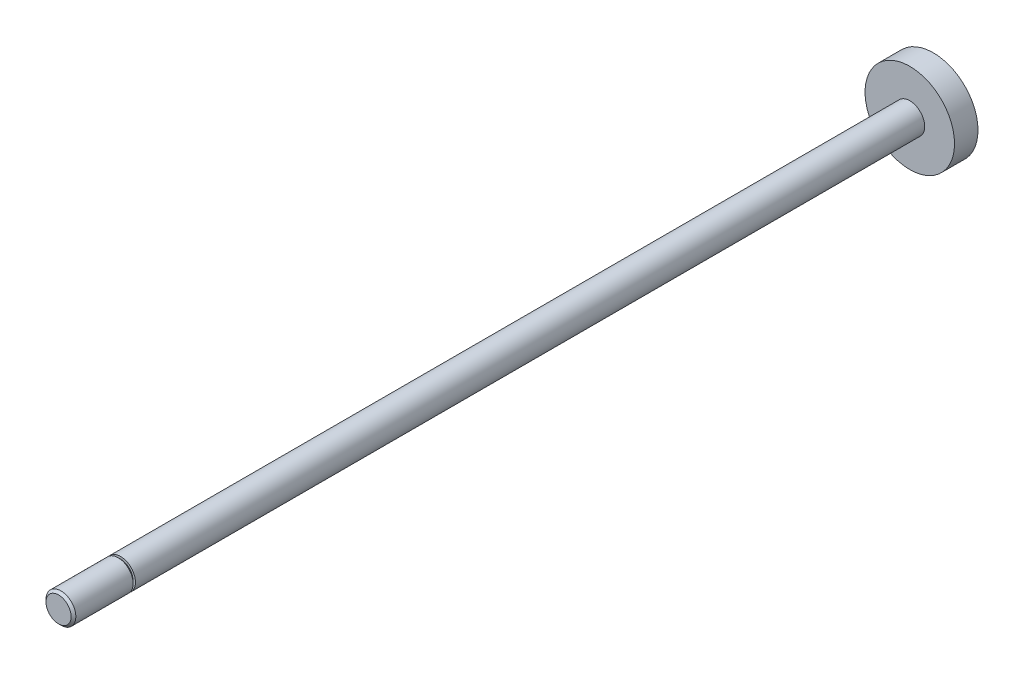
SolidWorks part; units mm, degrees
ref_plane "Front" through (0, 0, 0) normal (0, 0, 1) x (1, 0, 0)
ref_plane "Top" through (0, 0, 0) normal (0, 1, 0) x (1, 0, 0)
ref_plane "Right" through (0, 0, 0) normal (1, 0, 0) x (0, 0, -1)
sketch "Sketch1" plane through (0, 0, 0) normal (0, 0, 1) x (1, 0, 0)
  circle A0 centre (0, 0) radius 3.175
  dimension "MM" = 6.35
extrude "Extrude1" add sketch "Sketch1" along normal up to surface (183.769 mm away)
sketch "Sketch2" plane through (0, 0, 0) normal (0, 0, 1) x (1, 0, 0)
  circle A0 centre (0, 0) radius 9.525
  dimension "Bore" = 19.05
extrude "Piston" add sketch "Sketch2" along normal mid plane 5
sketch "Sketch3" plane through (0, 0, 0) normal (1, 0, 0) x (0, 0, -1)
  line L0 (-183.769, 9.525) -> (-170.569, 9.525)
  line L1 (-183.769, 9.525) -> (-183.769, 2.675)
  line L2 (-183.769, 2.675) -> (-183.269, 3.175)
  line L3 (-183.269, 3.175) -> (-171.069, 3.175)
  line L4 (-171.069, 3.175) -> (-171.069, 2.675)
  line L5 (-171.069, 2.675) -> (-170.569, 2.675)
  line L6 (-170.569, 2.675) -> (-170.569, 9.525)
  line L8 (-183.769, 3.175) -> (-183.769, -3.175) construction
  line L9 (2.5, 9.525) -> (-2.5, 9.525) construction
  line L10 (0, 0) -> (-105.1844, 0) construction
  dimension "D1" = 45
  dimension "KK" = 6.35
  dimension "D2" = 0.5
  dimension "D3" = 0.5
  dimension "D4" = 0.5
  dimension "A" = 12.7
revolve "Threads" cut sketch "Sketch3" angle 360 about L10
sketch "Sketch4" [suppressed] plane through (0, 0, 0) normal (0, 1, 0) x (1, 0, 0)
  line L0 (0, 0) -> (0, -104.7006) construction
  line L1 (7.9375, -174.879) -> (6.35, -174.879)
  line L2 (7.9375, -174.879) -> (-7.9375, -174.879) construction
  line L3 (6.35, -174.879) -> (6.35, -165.277)
  line L4 (6.35, -165.277) -> (7.9375, -163.6895)
  line L5 (7.9375, -163.6895) -> (7.9375, -174.879)
  line L6 (7.9375, -171.577) -> (7.9375, -2.5) construction
  line L7 (-7.9375, -163.6895) -> (-7.9375, -174.879)
  line L8 (-6.35, -165.277) -> (-7.9375, -163.6895)
  line L9 (-6.35, -174.879) -> (-6.35, -165.277)
  line L10 (-7.9375, -174.879) -> (-6.35, -174.879)
  dimension "D" = 6.35
  dimension "K" = 3.048
extrude "Flats" [suppressed] cut sketch "Sketch4" against normal through all and the other way through all
